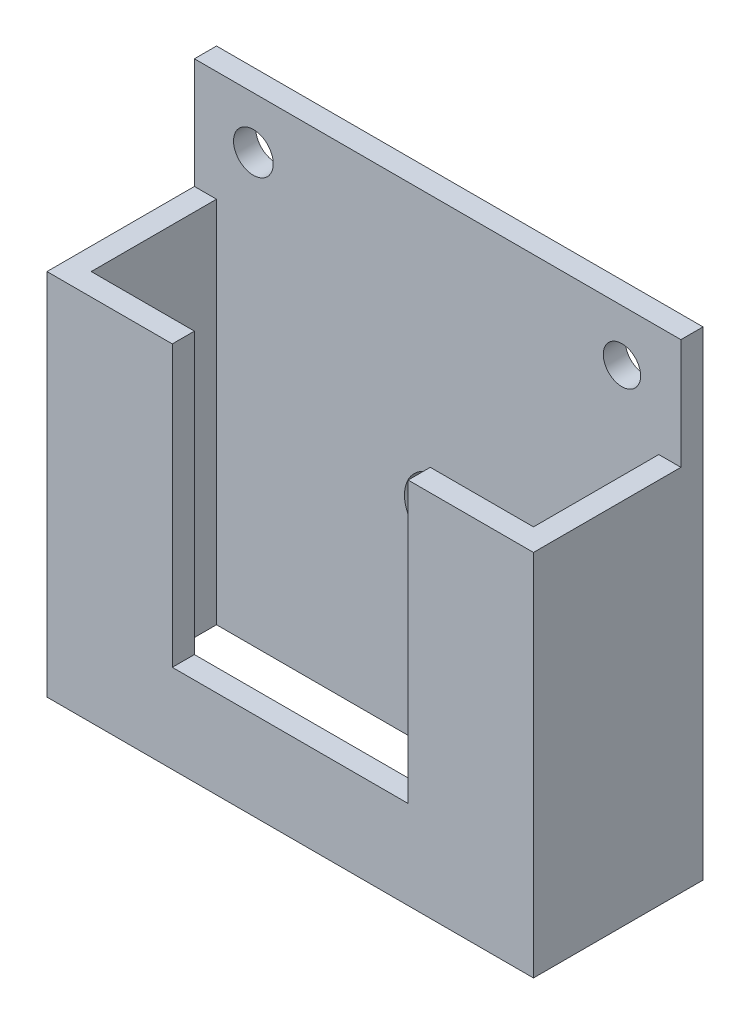
SolidWorks part; units mm, degrees
ref_plane "Front Plane" through (0, 0, 0) normal (0, 0, 1) x (1, 0, 0)
ref_plane "Top Plane" through (0, 0, 0) normal (0, 1, 0) x (1, 0, 0)
ref_plane "Right Plane" through (0, 0, 0) normal (1, 0, 0) x (0, 0, -1)
sketch "Sketch1" plane through (0, 0, 0) normal (1, 0, 0) x (0, 0, -1)
  line L0 (0, 0) -> (0, -65)
  line L1 (0, -65) -> (-23, -65)
  line L2 (-23, -65) -> (-23, 0)
  line L3 (-23, 0) -> (0, 0)
  dimension "D1" = 65
  dimension "D2" = 23
extrude "Boss-Extrude1" add sketch "Sketch1" against normal blind 66
sketch "Sketch2" plane through (0, 0, 0) normal (0, 1, 0) x (1, 0, 0)
  line L0 (-33, 0) -> (-33, -23) construction
  line L1 (-66, 0) -> (0, 0) construction
  line L2 (-66, -23) -> (0, -23) construction
  line L3 (-66, -11.5) -> (0, -11.5) construction
  line L4 (-66, 0) -> (-66, -23) construction
  line L5 (0, 0) -> (0, -23) construction
  line L7 (-63, -20) -> (-3, -20)
  line L8 (-63, -20) -> (-63, -3)
  line L9 (-63, -3) -> (-3, -3)
  line L10 (-3, -20) -> (-3, -3)
  line L11 (-63, -20) -> (-3, -3) construction
  line L12 (-63, -3) -> (-3, -20) construction
  point P12 (-33, -11.5)
  point P17 (-3, -11.5)
  point P18 (-63, -11.5)
  dimension "D1" = 3
  dimension "D2" = 3
  dimension "D3" = 3
  dimension "D4" = 3
extrude "Cut-Extrude1" cut sketch "Sketch2" against normal through all
sketch "Sketch3" plane through (0, 0, 23) normal (0, 0, 1) x (1, 0, 0)
  line L0 (-66, 0) -> (0, 0) construction
  line L1 (-49, 0) -> (-17, 0)
  line L2 (-49, 0) -> (-49, -53)
  line L3 (-49, -53) -> (-17, -53)
  line L4 (-17, 0) -> (-17, -53)
  line L5 (-66, 0) -> (-66, -65) construction
  line L6 (0, 0) -> (0, -65) construction
  line L7 (-66, -65) -> (0, -65) construction
  dimension "D1" = 17
  dimension "D2" = 17
  dimension "D3" = 32
  dimension "D4" = 12
  dimension "D5" = 53
extrude "Cut-Extrude2" cut sketch "Sketch3" against normal up to next
sketch "Sketch5" plane through (0, 0, 0) normal (0, 0, -1) x (-1, 0, 0)
  line L0 (33, -65) -> (33, 0) construction
  line L1 (66, -65) -> (0, -65) construction
  line L2 (66, 0) -> (0, 0) construction
  line L3 (0, -32.5) -> (66, -32.5) construction
  line L4 (0, -65) -> (0, 0) construction
  line L5 (66, -65) -> (66, 0) construction
  circle A0 centre (33, -37) radius 4.5
  circle A1 centre (8, -7) radius 2.5306
  circle A2 centre (58, -7) radius 2.6928
  dimension "D2" = 9
  dimension "D1" = 28
  dimension "D3" = 8
  dimension "D4" = 8
  dimension "D5" = 7
  dimension "D6" = 7
extrude "Cut-Extrude3" cut sketch "Sketch5" against normal up to next
sketch "Sketch6" plane through (0, 0, 23) normal (0, 0, 1) x (1, 0, 0)
  line L0 (-49, 0) -> (-49, -53) construction
  line L1 (-66, 0) -> (-49, 0)
  line L2 (-66, 0) -> (-66, -15)
  line L3 (-66, -15) -> (-49, -15)
  line L4 (-49, 0) -> (-49, -15)
  line L5 (0, 0) -> (0, -65) construction
  line L6 (-17, 0) -> (0, 0)
  line L7 (-17, 0) -> (-17, -15)
  line L8 (-17, -15) -> (0, -15)
  line L9 (0, 0) -> (0, -15)
  dimension "D1" = 15
  dimension "D2" = 15
  dimension "D3" = 17
  dimension "D4" = 17
extrude "Cut-Extrude4" cut sketch "Sketch6" against normal up to surface (20 mm away) up to face at (-37.5, -37, 3)
